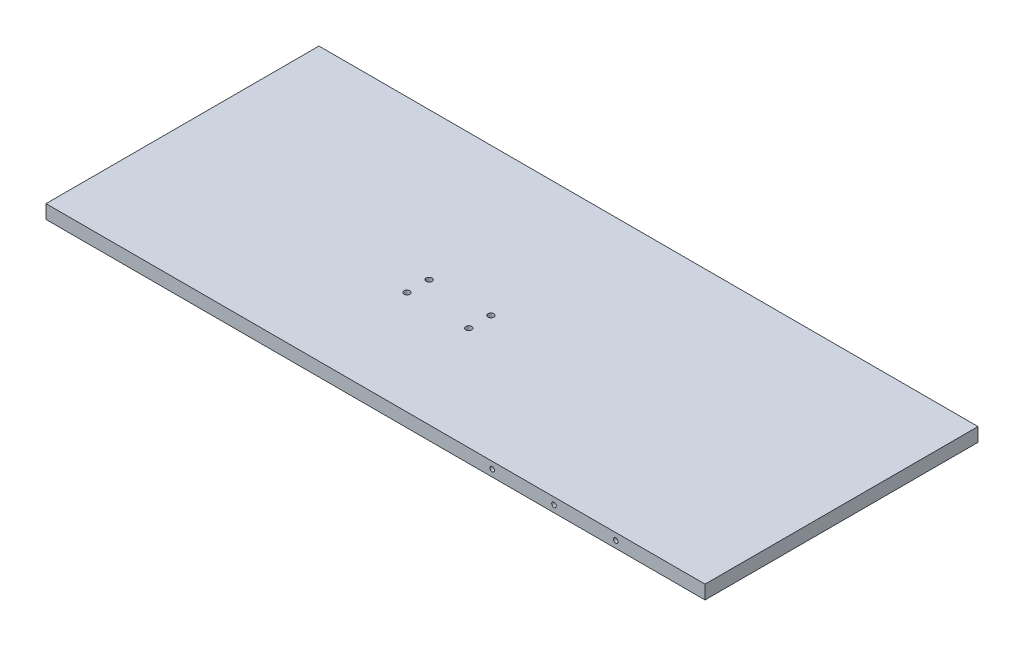
SolidWorks part; units mm, degrees
ref_plane "Front Plane" through (0, 0, 0) normal (0, 0, 1) x (1, 0, 0)
ref_plane "Top Plane" through (0, 0, 0) normal (0, 1, 0) x (1, 0, 0)
ref_plane "Right Plane" through (0, 0, 0) normal (1, 0, 0) x (0, 0, -1)
sketch "Sketch1" plane through (0, 0, 0) normal (0, 1, 0) x (1, 0, 0)
  line L1 (-1219.2, 0) -> (0, 0)
  line L2 (-1219.2, 0) -> (-1219.2, 505)
  line L3 (-1219.2, 505) -> (0, 505)
  line L4 (0, 0) -> (0, 505)
  line L5 (-1219.2, 0) -> (0, 505) construction
  line L6 (-1219.2, 505) -> (0, 0) construction
  point P0 (0, 0)
  dimension "D1" = 505
  dimension "D2" = 1219.2
extrude "Boss-Extrude1" add sketch "Sketch1" along normal blind 25.4
sketch "Sketch2" plane through (0, 0, 0) normal (0, 0, 1) x (1, 0, 0)
  line L0 (-1219.2, 0) -> (0, 0) construction
  line L1 (-406.4, 0) -> (-152.4, 0)
  line L2 (-406.4, 0) -> (-406.4, 25.4)
  line L3 (-406.4, 25.4) -> (-152.4, 25.4)
  line L4 (-152.4, 0) -> (-152.4, 25.4)
  line L5 (-1219.2, 25.4) -> (0, 25.4) construction
  line L7 (-406.4, 12.7) -> (-152.4, 12.7) construction
  line L8 (0, 25.4) -> (0, 0) construction
  point P13 (-279.4, 12.7)
  point P14 (-393.7, 12.7)
  point P15 (-165.1, 12.7)
  dimension "D1" = 152.4
  dimension "D2" = 254
  dimension "D3" = 12.7
  dimension "D4" = 12.7
hole_wizard "Tap Drill for M10x1.5 Tap1" positions "Sketch4" profile "Sketch3" hole size "M10x1.5" standard "ANSI Metric"
sketch "Sketch4" plane through (0, 0, 0) normal (0, 0, 1) x (1, 0, 0)
  line L0 (-406.4, 12.7) -> (-152.4, 12.7) construction
  point P0 (-393.7, 12.7)
  point P3 (-279.4, 12.7)
  point P7 (-165.1, 12.7)
sketch "Sketch3" plane through (-393.7, 12.7, 0) normal (1, 0, 0) x (0, -1, 0)
  line L0 (0, 0) -> (0, 22.5537)
  line L1 (0, 22.5537) -> (4.25, 20)
  line L2 (4.25, 20) -> (4.25, 0)
  line L5 (4.25, 0) -> (0, 0)
  line L10 (0, 22.5537) -> (-4.25, 20) construction
  line L11 (0, -6.35) -> (0, 107.95) construction
  dimension "Hole Dia." = 8.5
  dimension "Hole Depth" = 20
  dimension "Drill Angle" = 118
sketch "Sketch5" plane through (0, 0, -505) normal (0, 0, -1) x (-1, 0, 0)
  point P0 (165.1, 12.7)
  point P1 (279.4, 12.7)
  point P3 (393.7, 12.7)
hole_wizard "Tap Drill for M10x1.5 Tap2" positions "Sketch8" profile "Sketch6" hole size "M10x1.5" standard "ANSI Metric"
sketch "Sketch8" plane through (0, 0, -505) normal (0, 0, -1) x (-1, 0, 0)
  point P0 (165.1, 12.7)
  point P3 (279.4, 12.7)
  point P6 (393.7, 12.7)
sketch "Sketch6" plane through (-165.1, 12.7, -505) normal (1, 0, 0) x (0, 1, 0)
  line L0 (0, 0) -> (0, 22.5537)
  line L1 (0, 22.5537) -> (4.25, 20)
  line L2 (4.25, 20) -> (4.25, 0)
  line L5 (4.25, 0) -> (0, 0)
  line L10 (0, 22.5537) -> (-4.25, 20) construction
  line L11 (0, -6.35) -> (0, 107.95) construction
  dimension "Hole Dia." = 8.5
  dimension "Hole Depth" = 20
  dimension "Drill Angle" = 118
sketch "Sketch12" plane through (0, 25.4, 0) normal (0, 1, 0) x (1, 0, 0)
  line L0 (-1219.2, 252.5) -> (0, 252.5) construction
  line L1 (-1219.2, 505) -> (-1219.2, 0) construction
  line L2 (0, 0) -> (0, 505) construction
  line L3 (-609.6, 505) -> (-609.6, 0) construction
  line L4 (0, 505) -> (-1219.2, 505) construction
  line L5 (-1219.2, 0) -> (0, 0) construction
sketch "Sketch14" plane through (0, 0, 0) normal (0, 0, 1) x (1, 0, 0)
  line L0 (-18.7223, -104.0765) -> (-18.7223, -170.3765)
  line L1 (0.2777, -116.7765) -> (114.6777, -116.7765)
  line L2 (0.2777, -116.7765) -> (0.2777, -157.6765)
  line L3 (0.2777, -157.6765) -> (114.6777, -157.6765)
  line L4 (114.6777, -116.7765) -> (114.6777, -157.6765)
  line L5 (-18.7223, -170.3765) -> (19.7777, -170.3765)
  line L6 (19.7777, -170.3765) -> (19.7777, -177.6765)
  line L7 (19.7777, -177.6765) -> (133.895, -177.6765)
sketch "Sketch15" plane through (0, 25.4, 0) normal (0, 1, 0) x (1, 0, 0)
  line L0 (-279.4, 0) -> (-279.4, 505) construction
  line L1 (-433.07, 0) -> (-433.07, 505) construction
  line L2 (-1219.2, 0) -> (0, 0) construction
  line L3 (0, 505) -> (-1219.2, 505) construction
  line L4 (-560.07, 0) -> (-560.07, 505) construction
  dimension "D1" = 153.67
  dimension "D2" = 127
ref_plane "Plane1" through (0, 0, -252.5) normal (0, 0, 1) x (1, 0, 0)
sketch "Sketch16" plane through (0, 25.4, 0) normal (0, 1, 0) x (1, 0, 0)
  line L1 (-628.6, 191.6) -> (-743, 191.6)
  line L2 (-628.6, 191.6) -> (-628.6, 232.5)
  line L3 (-628.6, 232.5) -> (-743, 232.5)
  line L4 (-743, 191.6) -> (-743, 232.5)
hole_wizard "M10 Clearance Hole1" positions "Sketch18" profile "Sketch19" hole size "M10" standard "ANSI Metric" end condition through all
sketch "Sketch18" plane through (0, 25.4, 0) normal (0, 1, 0) x (1, 0, 0)
  point P0 (-628.6, 191.6)
  point P3 (-628.6, 232.5)
  point P6 (-743, 232.5)
  point P9 (-743, 191.6)
sketch "Sketch19" plane through (-628.6, 25.4, -191.6) normal (1, 0, 0) x (0, 0, 1)
  line L0 (0, 0) -> (0, 25.4)
  line L1 (0, 25.4) -> (5.5, 25.4)
  line L2 (5.5, 25.4) -> (5.5, 0)
  line L5 (5.5, 0) -> (0, 0)
  line L11 (0, -6.35) -> (0, 107.95) construction
  dimension "Thru Hole Dia." = 11
  dimension "Thru Hole Depth" = 25.4
